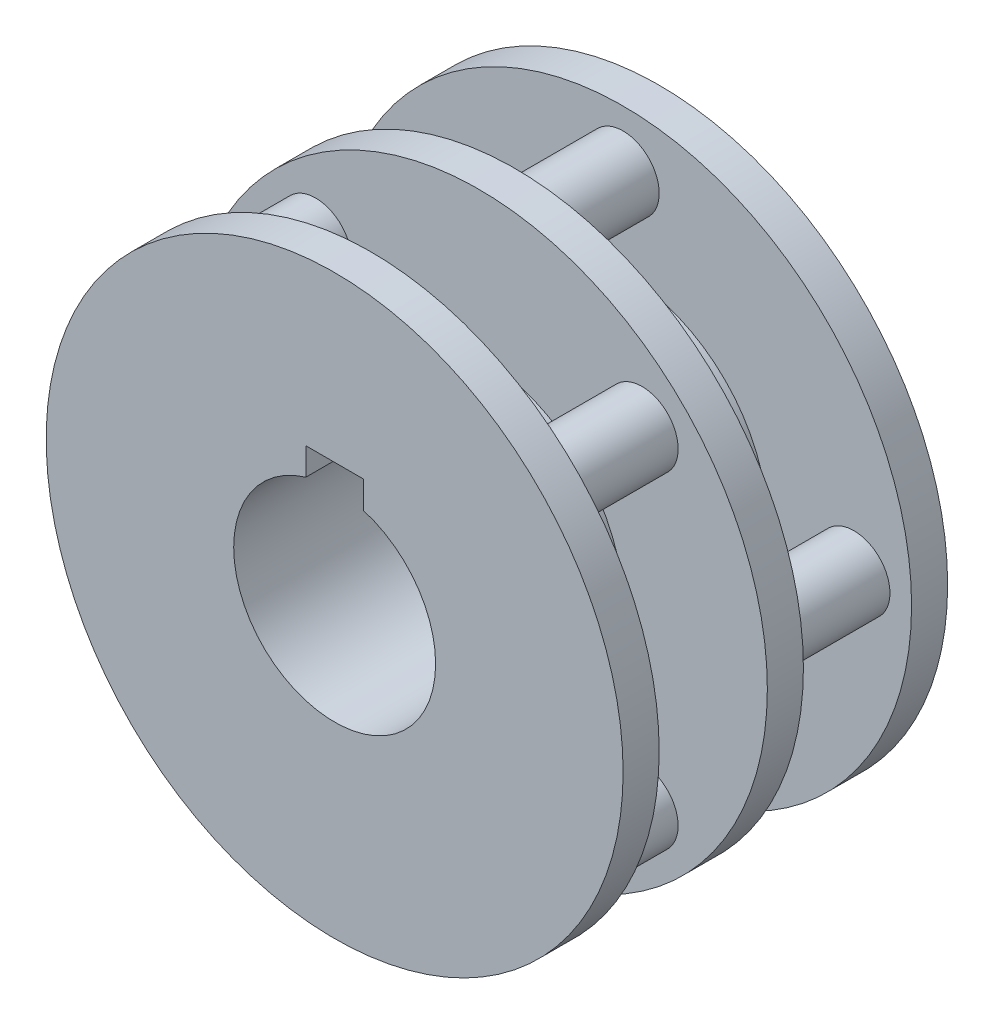
SolidWorks part; units mm, degrees
ref_plane "前视基准面" through (0, 0, 0) normal (0, 0, 1) x (1, 0, 0)
ref_plane "上视基准面" through (0, 0, 0) normal (0, 1, 0) x (1, 0, 0)
ref_plane "右视基准面" through (0, 0, 0) normal (1, 0, 0) x (0, 0, -1)
sketch "草图1" plane through (0, 0, 0) normal (0, 0, 1) x (1, 0, 0)
  circle A0 centre (0, 0) radius 40
  dimension "D1" = 80
extrude "凸台-拉伸1" add sketch "草图1" along normal blind 5
sketch "草图2" plane through (0, 0, 5) normal (0, 0, 1) x (1, 0, 0)
  circle A0 centre (32, 0) radius 5
  circle A1 centre (0, -32) radius 5
  circle A2 centre (-32, 0) radius 5
  circle A3 centre (0, 32) radius 5
  dimension "D1" = 32
  dimension "D2" = 10
  dimension "D3" = 4
extrude "凸台-拉伸2" add sketch "草图2" along normal blind 15
sketch "草图3" plane through (0, 0, 20) normal (0, 0, 1) x (1, 0, 0)
  circle A0 centre (0, 0) radius 40
  dimension "D1" = 80
extrude "凸台-拉伸3" add sketch "草图3" along normal blind 5
sketch "草图4" plane through (0, 0, 25) normal (0, 0, 1) x (1, 0, 0)
  circle A1 centre (22.6274, -22.6274) radius 5
  circle A3 centre (-22.6274, -22.6274) radius 5
  circle A5 centre (-22.6274, 22.6274) radius 5
  circle A7 centre (22.6274, 22.6274) radius 5
  circle A8 centre (32, 0) radius 5
  circle A9 centre (-32, 0) radius 5
  circle A10 centre (0, -32) radius 5
  circle A11 centre (0, 32) radius 5
  dimension "D2" = 32
extrude "凸台-拉伸4" add sketch "草图4" along normal blind 15
sketch "草图5" plane through (0, 0, 40) normal (0, 0, 1) x (1, 0, 0)
  circle A0 centre (0, 0) radius 40
  dimension "D1" = 80
extrude "凸台-拉伸5" add sketch "草图5" along normal blind 5
sketch "草图6" plane through (0, 0, 5) normal (0, 0, 1) x (1, 0, 0)
  circle A0 centre (0, 0) radius 20
  dimension "D1" = 40
extrude "凸台-拉伸6" add sketch "草图6" along normal up to surface (35 mm away) up to face at (-17.6274, -22.6274, 40)
sketch "草图7" plane through (0, 0, 45) normal (0, 0, 1) x (1, 0, 0)
  circle A0 centre (0, 0) radius 14
  dimension "D1" = 28
extrude "切除-拉伸1" cut sketch "草图7" against normal blind 57
sketch "草图8" plane through (0, 0, 45) normal (0, 0, 1) x (1, 0, 0)
  line L0 (0, 14) -> (11.7512, 14) construction
  line L1 (-4, 14) -> (-4, 9.3949)
  line L3 (4, 14) -> (4, 17.2)
  line L4 (4, 17.2) -> (-4, 17.2)
  line L5 (-4, 14) -> (-4, 17.2)
  line L6 (-4, 9.3949) -> (4, 9.3949)
  line L7 (4, 9.3949) -> (4, 14)
  circle A0 centre (0, 0) radius 14 construction
  dimension "D2" = 4
  dimension "D3" = 4
extrude "切除-拉伸2" cut sketch "草图8" against normal blind 57
